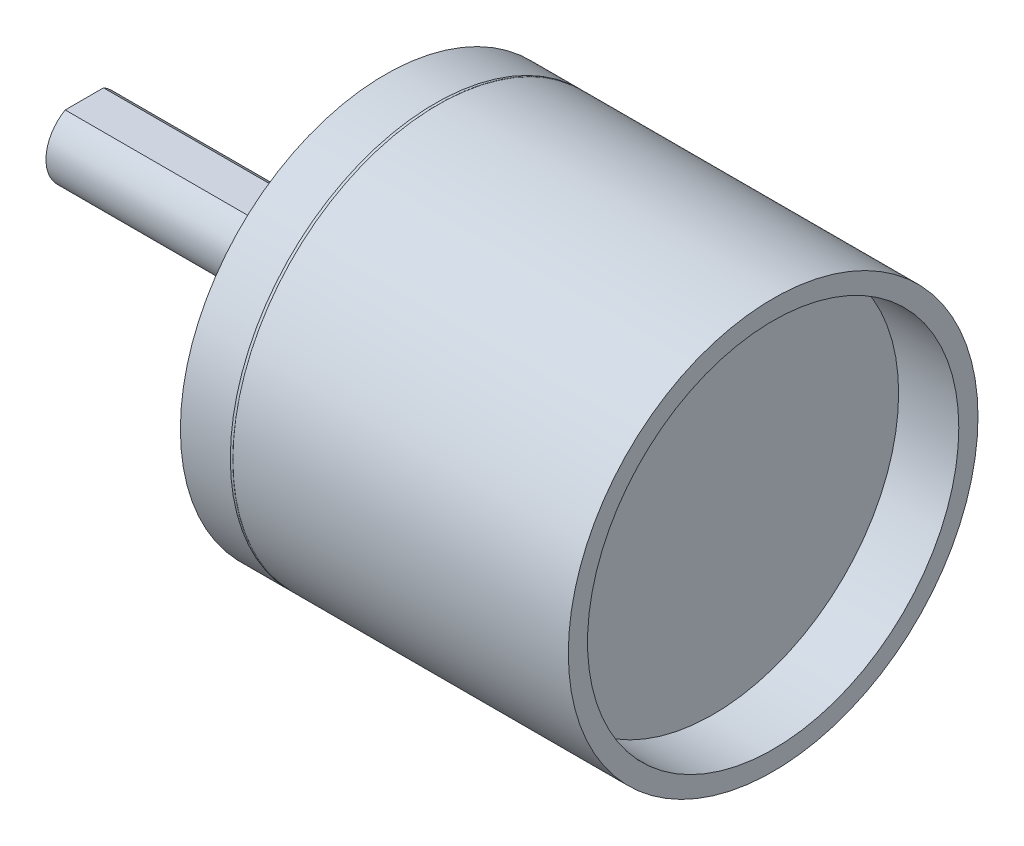
SolidWorks part; units mm, degrees
ref_plane "Front Plane" through (0, 0, 0) normal (0, 0, 1) x (1, 0, 0)
ref_plane "Top Plane" through (0, 0, 0) normal (0, 1, 0) x (1, 0, 0)
ref_plane "Right Plane" through (0, 0, 0) normal (1, 0, 0) x (0, 0, -1)
sketch "Sketch1" plane through (0, 0, 0) normal (0, 0, 1) x (1, 0, 0)
  line L0 (0, 8) -> (0, 0)
  line L1 (0, 0) -> (15.15, 0)
  line L2 (15.15, 0) -> (15.15, 8)
  line L3 (15.15, 8) -> (2.05, 8)
  line L4 (1.95, 8) -> (0, 8)
  line L5 (0, 0) -> (15.15, 0) construction
  arc A0 (2.05, 8) -> (1.95, 8) centre (2, 8.0866) cw
revolve "Revolve1" add sketch "Sketch1" angle 360 about L5
sketch "Sketch2" plane through (0, 0, 0) normal (-1, 0, 0) x (0, 0, 1)
  circle A0 centre (0, 0) radius 3
extrude "Boss-Extrude1" add sketch "Sketch2" along normal blind 1
sketch "Sketch3" plane through (-1, 0, 0) normal (-1, 0, 0) x (0, 0, 1)
  circle A0 centre (0, 0) radius 2.5
extrude "Boss-Extrude2" add sketch "Sketch3" along normal blind 1.6
sketch "Sketch4" plane through (-2.6, 0, 0) normal (-1, 0, 0) x (0, 0, 1)
  circle A0 centre (0, 0) radius 1.5
extrude "Boss-Extrude3" add sketch "Sketch4" along normal blind 9.15
sketch "Sketch5" plane through (-11.75, 0, 0) normal (-1, 0, 0) x (0, 0, 1)
  line L0 (-0.7483, 1.3) -> (0.7483, 1.3)
  arc A0 (0.7483, 1.3) -> (-0.7483, 1.3) centre (0, 0) ccw
extrude "Cut-Extrude1" cut sketch "Sketch5" against normal blind 7.8
draft "Draft1" type of draft neutral plane draft angle 44.5 faces to draft 1 face at (-3.95, 1.4, 0) neutral plane through (-3.95, 1.3, -0.7483) neutral plane normal (0, 1, 0) parameters "D1"=44.5
hole_wizard "Ø14.5 (14.5) Diameter Hole1" positions "Sketch7" profile "Sketch6" hole size "Ø14.5" standard "ANSI Metric"
sketch "Sketch7" plane through (15.15, 0, 0) normal (1, 0, 0) x (0, 0, -1)
  point P0 (0, 0)
sketch "Sketch6" plane through (15.15, 0, 0) normal (0, 1, 0) x (0, 0, -1)
  line L0 (0, 0) -> (0, 2.35)
  line L1 (0, 2.35) -> (7.25, 2.35)
  line L2 (7.25, 2.35) -> (7.25, 0)
  line L5 (7.25, 0) -> (0, 0)
  line L10 (0, 2.35) -> (-7.25, 2.35) construction
  line L11 (0, -6.35) -> (0, 107.95) construction
  dimension "Hole Dia." = 14.5
  dimension "Hole Depth" = 2.35
  dimension "Drill Angle" = 180
hole_wizard "Ø1.6 (1.6) Diameter Hole1" positions "Sketch9" profile "Sketch8" hole size "Ø1.6" standard "ANSI Metric"
sketch "Sketch9" plane through (0, 0, 0) normal (-1, 0, 0) x (0, 0, 1)
  point P0 (0, 5)
  point P1 (4.3301, 2.5)
  point P2 (4.3301, -2.5)
  point P3 (0, -5)
  point P4 (-4.3301, -2.5)
  point P5 (-4.3301, 2.5)
sketch "Sketch8" plane through (0, 5, 0) normal (0, 1, 0) x (0, 0, 1)
  line L0 (0, 0) -> (0, 3.4807)
  line L1 (0, 3.4807) -> (0.8, 3)
  line L2 (0.8, 3) -> (0.8, 0)
  line L5 (0.8, 0) -> (0, 0)
  line L10 (0, 3.4807) -> (-0.8, 3) construction
  line L11 (0, -6.35) -> (0, 107.95) construction
  dimension "Hole Dia." = 1.6
  dimension "Hole Depth" = 3
  dimension "Drill Angle" = 118
